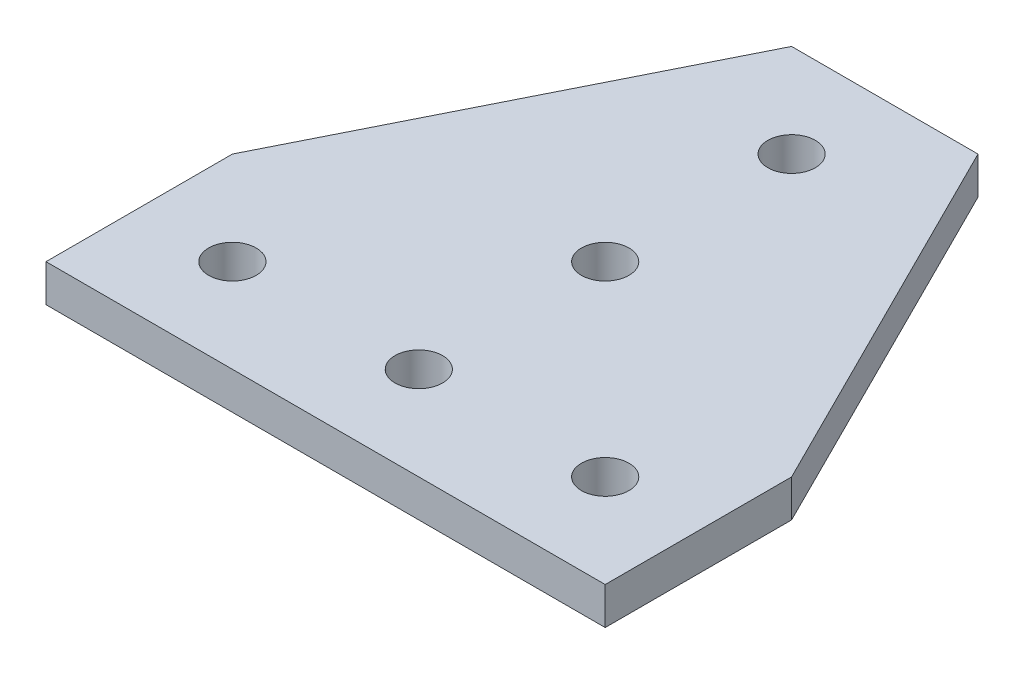
SolidWorks part; units mm, degrees
material "6061-T6 (SS)"
ref_plane "Front Plane" through (0, 0, 0) normal (0, 0, 1) x (1, 0, 0)
ref_plane "Top Plane" through (0, 0, 0) normal (0, 1, 0) x (1, 0, 0)
ref_plane "Right Plane" through (0, 0, 0) normal (1, 0, 0) x (0, 0, -1)
sketch "Sketch1" plane through (0, 0, 0) normal (0, 1, 0) x (1, 0, 0)
  line L0 (-30, 0) -> (0, 0) construction
  line L1 (30, -10) -> (-30, -10)
  line L2 (-10, 50) -> (10, 50)
  line L3 (0, 0) -> (0, 50) construction
  line L4 (-30, -10) -> (-30, 10)
  line L5 (0, 0) -> (-20, 0) construction
  line L6 (0, 0) -> (0, 20) construction
  line L7 (-30, 10) -> (-10, 50)
  line L8 (30, -10) -> (30, 10)
  line L9 (0, 0) -> (20, 0) construction
  line L10 (30, 10) -> (10, 50)
  circle A0 centre (-20, 0) radius 2.55
  circle A1 centre (20, 0) radius 2.55
  circle A2 centre (0, 0) radius 2.55
  circle A3 centre (0, 20) radius 2.55
  circle A4 centre (0, 40) radius 2.55
  point P15 (0, -10)
  dimension "D3" = 2
  dimension "D2" = 5.1
  dimension "D1" = 20
  dimension "D4" = 20
  dimension "D5" = 60
  dimension "D7" = 20
  dimension "D9" = 20
  dimension "D10" = 60
  dimension "D11" = 20
  dimension "D6" = 3
  dimension "D8" = 2
extrude "Boss-Extrude1" add sketch "Sketch1" along normal blind 4
